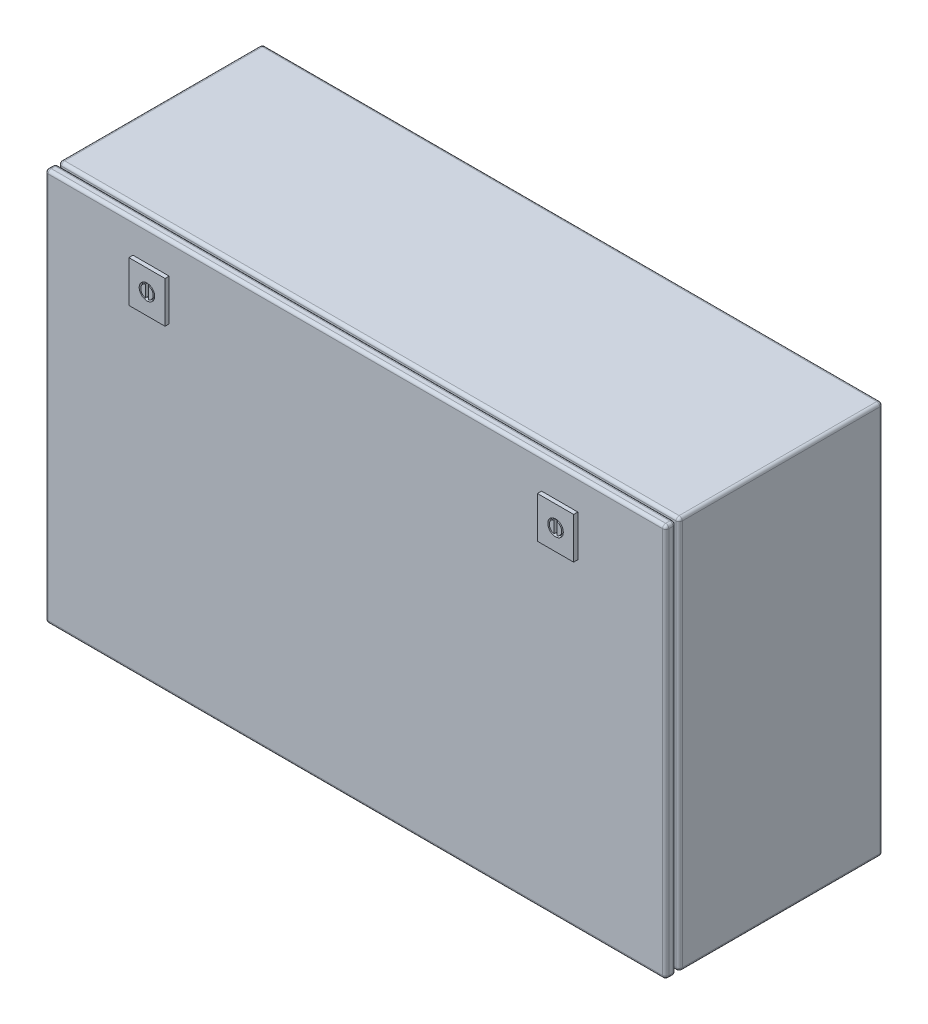
SolidWorks part; units mm, degrees
ref_plane "Front Plane" through (0, 0, 0) normal (0, 0, 1) x (1, 0, 0)
ref_plane "Top Plane" through (0, 0, 0) normal (0, 1, 0) x (1, 0, 0)
ref_plane "Right Plane" through (0, 0, 0) normal (1, 0, 0) x (0, 0, -1)
sketch "Sketch1" plane through (0, 0, 0) normal (0, 0, 1) x (1, 0, 0)
  line L1 (0, 0) -> (600, 0)
  line L2 (0, 0) -> (0, 380)
  line L3 (0, 380) -> (600, 380)
  line L4 (600, 0) -> (600, 380)
  dimension "D1" = 380
  dimension "D2" = 600
extrude "Boss-Extrude1" add sketch "Sketch1" along normal blind 210
ref_plane "Plane1" through (0, 0, 200) normal (0, 0, 1) x (1, 0, 0)
sketch "Sketch2" plane through (0, 0, 200) normal (0, 0, 1) x (1, 0, 0)
  line L1 (0, 0) -> (600, 0)
  line L2 (0, 0) -> (0, 380)
  line L3 (0, 380) -> (600, 380)
  line L4 (600, 0) -> (600, 380)
  line L5 (10, 370) -> (590, 370)
  line L6 (10, 370) -> (10, 10)
  line L7 (10, 10) -> (590, 10)
  line L8 (590, 370) -> (590, 10)
  dimension "D1" = 10
  dimension "D2" = 10
  dimension "D3" = 10
  dimension "D4" = 10
extrude "Cut-Extrude3" cut sketch "Sketch2" against normal blind 3
fillet "Fillet3" radius 3 24 edges at (300, 380, 0) (300, 380, 197) (0, 190, 0) (0, 380, 98.5) (0, 190, 197) (600, 190, 0) (600, 190, 197) (600, 380, 98.5) (300, 0, 0) (0, 0, 98.5) (300, 0, 197) (600, 0, 98.5) (300, 0, 200) (600, 0, 205) (600, 190, 200) (600, 380, 205) (300, 380, 200) (0, 380, 205) (0, 0, 205) (0, 190, 200) (300, 380, 210) (600, 190, 210) (300, 0, 210) (0, 190, 210)
sketch "Sketch4" plane through (0, 0, 210) normal (0, 0, 1) x (1, 0, 0)
  line L0 (300, 377) -> (300, -12.3786) construction
  line L1 (85, 350) -> (120, 350)
  line L2 (85, 350) -> (85, 310)
  line L3 (85, 310) -> (120, 310)
  line L4 (120, 350) -> (120, 310)
  line L5 (597, 377) -> (3, 377) construction
  line L6 (0, 3) -> (0, 377) construction
  line L7 (3, 380) -> (597, 380) construction
  line L8 (480, 350) -> (480, 310)
  line L9 (515, 310) -> (480, 310)
  line L10 (515, 350) -> (515, 310)
  line L11 (515, 350) -> (480, 350)
  dimension "D1" = 35
  dimension "D2" = 40
  dimension "D3" = 85
  dimension "D4" = 30
extrude "Boss-Extrude3" add sketch "Sketch4" along normal blind 4
sketch "Sketch5" plane through (0, 0, 214) normal (0, 0, 1) x (1, 0, 0)
  line L0 (120, 350) -> (85, 350) construction
  line L1 (300, 380) -> (300, 163.6701) construction
  line L2 (3, 380) -> (597, 380) construction
  line L3 (496, 335.8095) -> (496, 324.1905)
  line L5 (101, 335.8095) -> (101, 324.1905)
  line L7 (104, 335.8095) -> (104, 324.1905)
  line L9 (499, 335.8095) -> (499, 324.1905)
  circle A0 centre (102.5, 330) radius 7.5
  circle A1 centre (497.5, 330) radius 7.5
  arc A2 (104, 324.1905) -> (104, 335.8095) centre (102.5, 330) ccw
  arc A3 (496, 324.1905) -> (496, 335.8095) centre (497.5, 330) cw
  circle A4 centre (497.5, 330) radius 7.5
  arc A5 (499, 335.8095) -> (499, 324.1905) centre (497.5, 330) cw
  arc A6 (101, 335.8095) -> (101, 324.1905) centre (102.5, 330) ccw
  point P5 (102.5, 350)
  point P11 (0, 0)
  dimension "D1" = 15
  dimension "D4" = 12
  dimension "D2" = 20
  dimension "D3" = 3
extrude "Cut-Extrude6" cut sketch "Sketch5" against normal blind 3 contours A0 A6 L5 A2 L7 | A1 L3 A3 L9 A5
